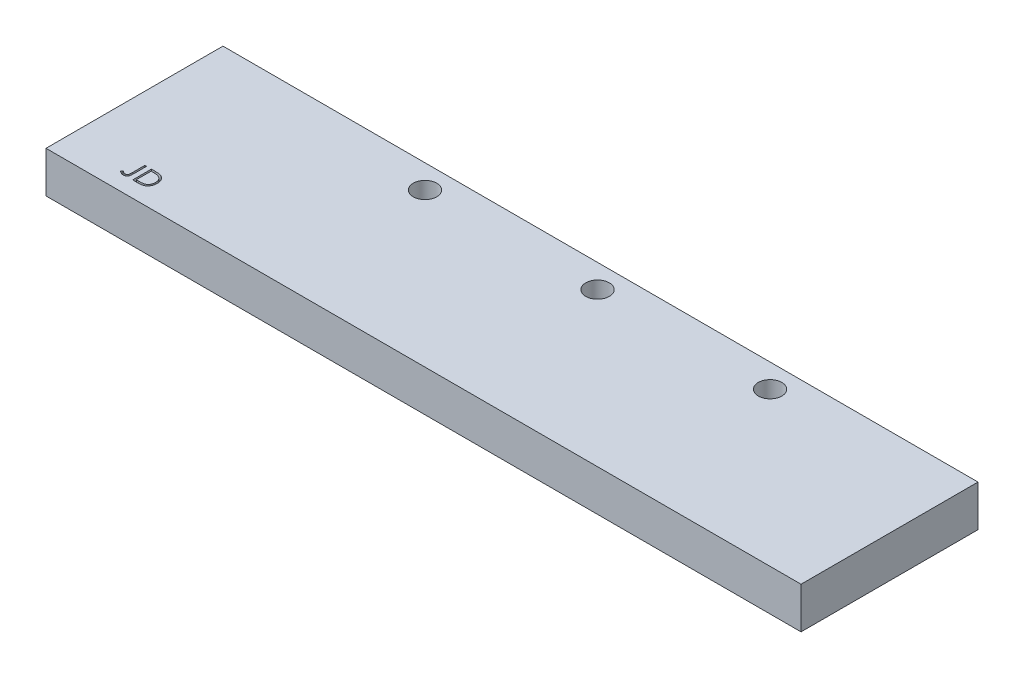
SolidWorks part; units mm, degrees
ref_plane "Front Plane" through (0, 0, 0) normal (0, 0, 1) x (1, 0, 0)
ref_plane "Top Plane" through (0, 0, 0) normal (0, 1, 0) x (1, 0, 0)
ref_plane "Right Plane" through (0, 0, 0) normal (1, 0, 0) x (0, 0, -1)
sketch "Sketch1" plane through (0, 0, 0) normal (0, 1, 0) x (1, 0, 0)
  line L1 (-102.5105, 65.1674) -> (25.4895, 65.1674)
  line L2 (-102.5105, 65.1674) -> (-102.5105, 35.1674)
  line L3 (-102.5105, 35.1674) -> (25.4895, 35.1674)
  line L4 (25.4895, 65.1674) -> (25.4895, 35.1674)
  dimension "D1" = 30
  dimension "D2" = 128
extrude "Boss-Extrude1" add sketch "Sketch1" along normal blind 7 contours L2 L3 L4 L1
sketch "Sketch2" plane through (0, 0, 0) normal (0, -1, 0) x (1, 0, 0)
  line L1 (-102.5105, -65.1674) -> (25.4895, -65.1674) construction
  line L3 (25.4895, -65.1674) -> (25.4895, -35.1674) construction
  circle A0 centre (-64.2605, -61.1674) radius 2
  circle A1 centre (-35.0105, -61.1674) radius 2
  circle A2 centre (-5.7605, -61.1674) radius 2
  dimension "D1" = 31.25
  dimension "D5" = 29.25
  dimension "D2" = 4
  dimension "D3" = 29.25
  dimension "D4" = 4
  dimension "D6" = 4
extrude "Cut-Extrude1" cut sketch "Sketch2" against normal blind 10
sketch "Sketch3" plane through (0, 7, 0) normal (0, 1, 0) x (1, 0, 0)
  text T0 "JD"
extrude "Cut-Extrude2" cut sketch "Sketch3" against normal blind 1
